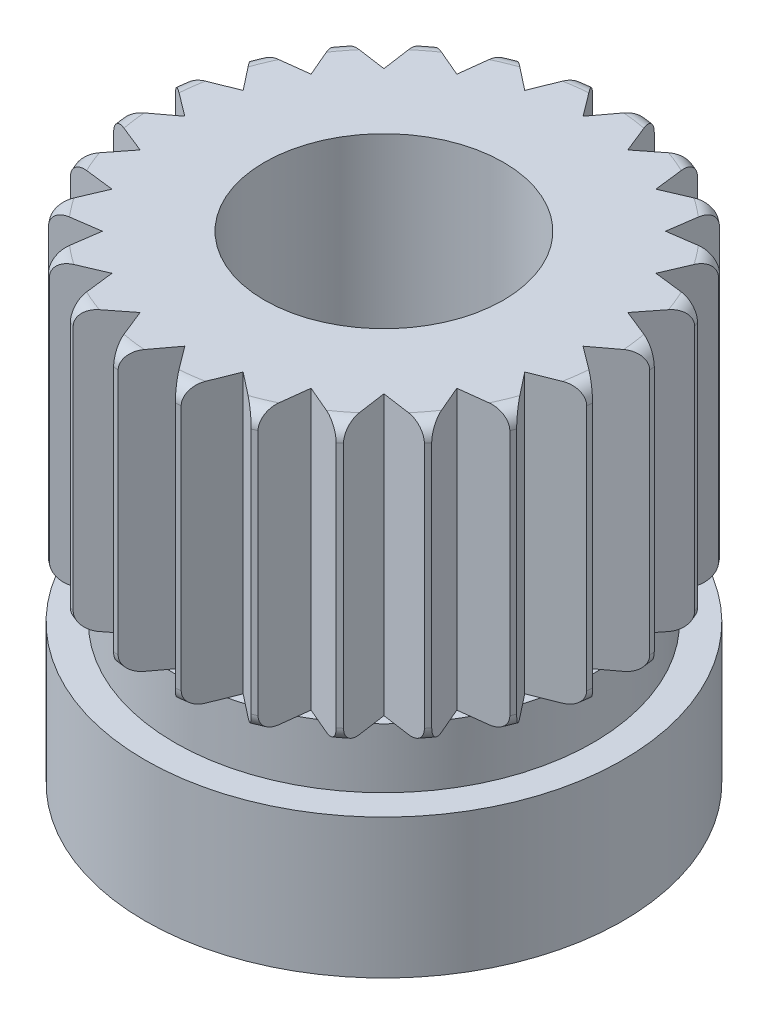
SolidWorks part; units mm, degrees
material "Brass"
ref_plane "Front Plane" through (0, 0, 0) normal (0, 0, 1) x (1, 0, 0)
ref_plane "Top Plane" through (0, 0, 0) normal (0, 1, 0) x (1, 0, 0)
ref_plane "Right Plane" through (0, 0, 0) normal (1, 0, 0) x (0, 0, -1)
sketch "Sketch1" plane through (0, 0, 0) normal (0, 0, 1) x (1, 0, 0)
  line L0 (12.8466, 60.7319) -> (9.8466, 60.7319)
  line L1 (12.8466, 54.7319) -> (12.8466, 56.4819)
  line L2 (12.8466, 56.4819) -> (12.4716, 56.4819)
  line L3 (12.4716, 56.4819) -> (12.4716, 57.2319)
  line L4 (12.4716, 57.2319) -> (12.8466, 57.2319)
  line L5 (12.8466, 57.2319) -> (12.8466, 60.7319)
  line L6 (9.8466, 60.7319) -> (9.8466, 54.7319)
  line L7 (9.8466, 54.7319) -> (12.8466, 54.7319)
  dimension "D1" = 3
  dimension "D2" = 3
  dimension "D3" = 2.625
  dimension "D4" = 0.75
  dimension "D5" = 3.5
  dimension "D6" = 1.75
revolve "Revolve1" add sketch "Sketch1" angle 360 about L6
fillet "Fillet4" radius 0.2 2 edges at (9.8466, 60.7319, 3) (9.8466, 57.2319, 3)
sketch "Sketch2" plane through (0, 60.7319, 0) normal (0, 1, 0) x (1, 0, 0)
  line L0 (9.8466, 0) -> (9.8466, 3.6508) construction
  line L1 (9.3966, 3.1) -> (9.8466, 2.5)
  line L2 (9.8466, 2.5) -> (10.2966, 3.1)
  line L3 (9.3966, 3.1) -> (10.2966, 3.1)
  point P0 (9.8466, 0)
  point P6 (9.8466, 3.1)
  dimension "D2" = 2.5
  dimension "D1" = 0.9
  dimension "D3" = 0.6
extrude "Cut-Extrude3" cut sketch "Sketch2" against normal up to surface (3.5 mm away) up to face at (9.8466, 57.2319, 2.8)
pattern_circular "CirPattern1" count 24 over 360 about axis through (9.8466, 0, 0) along (0, 1, 0) of "Cut-Extrude3"
sketch "Sketch3" plane through (0, 60.7319, 0) normal (0, 1, 0) x (1, 0, 0)
  circle A0 centre (9.8466, 0) radius 1.5
  dimension "D1" = 3
extrude "Cut-Extrude4" cut sketch "Sketch3" against normal blind 8
